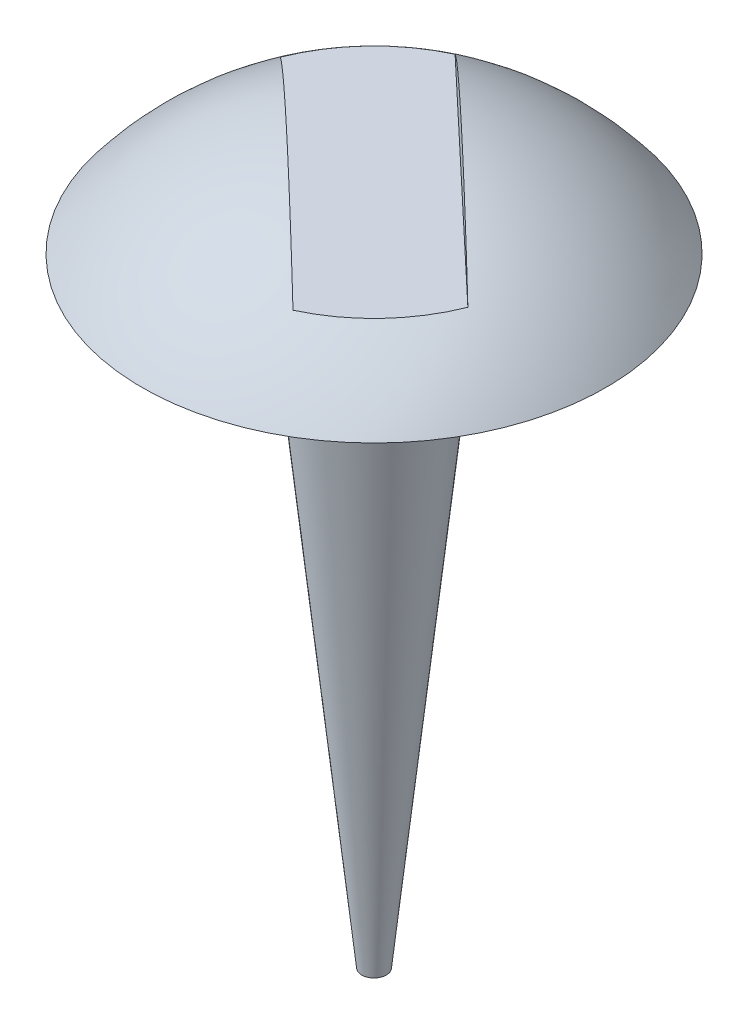
SolidWorks part; units mm, degrees
ref_plane "前视基准面" through (0, 0, 0) normal (0, 0, 1) x (1, 0, 0)
ref_plane "上视基准面" through (0, 0, 0) normal (0, 1, 0) x (1, 0, 0)
ref_plane "右视基准面" through (0, 0, 0) normal (1, 0, 0) x (0, 0, -1)
sketch "草图2" plane through (0, 0, 0) normal (0, 0, 1) x (1, 0, 0)
  line L0 (-0.3, 0) -> (0.3, 0)
  line L1 (0, -0.078) -> (0, 0.3092)
  arc A0 (0.3, 0) -> (-0.3, 0) centre (0, -0.2313) ccw
  dimension "D1" = 0.3
  dimension "D2" = 0.3
revolve "旋转1" add sketch "草图2" angle 360 about L1
sketch "草图3" plane through (0, 0, 0) normal (0, -1, 0) x (1, 0, 0)
  circle A0 centre (0, 0) radius 0.1
extrude "凸台-拉伸1" add sketch "草图3" along normal blind 0.8 draft 6
sketch "草图4" plane through (0, 0, 0) normal (0, -1, 0) x (1, 0, 0)
  circle A0 centre (0, 0) radius 0.1004
sketch "草图7" plane through (0, -0.8, 0) normal (0, -1, 0) x (1, 0, 0)
  circle A1 centre (0, 0) radius 0.0159
  circle A2 centre (0, 0) radius 0.0159
  dimension "D1" = 0
curve "螺旋线/涡状线2"
ref_plane "基准面1" through (0, 0.08, 0) normal (0, -1, 0) x (1, 0, 0)
sketch "草图8" plane through (0, 0.08, 0) normal (0, -1, 0) x (1, 0, 0)
  line L0 (0, 0) -> (-0.2482, -0.2341)
  line L1 (0, 0) -> (0.2514, 0.2372)
  line L2 (-0.0549, 0.0582) -> (0.1966, 0.2954)
  line L3 (-0.0549, 0.0582) -> (-0.3031, -0.1759)
  line L4 (0.0549, -0.0582) -> (0.3063, 0.179)
  line L5 (0.0549, -0.0582) -> (-0.1933, -0.2923)
  line L6 (0.1966, 0.2954) -> (0.3063, 0.179)
  line L7 (-0.3031, -0.1759) -> (-0.1933, -0.2923)
  dimension "D1" = 0.08
  dimension "D2" = 0.08
extrude "切除-拉伸1" cut sketch "草图8" against normal blind 5 contours L3 L7 L0 L1 L6 L2 | L0 L7 L5 L4 L6 L1
